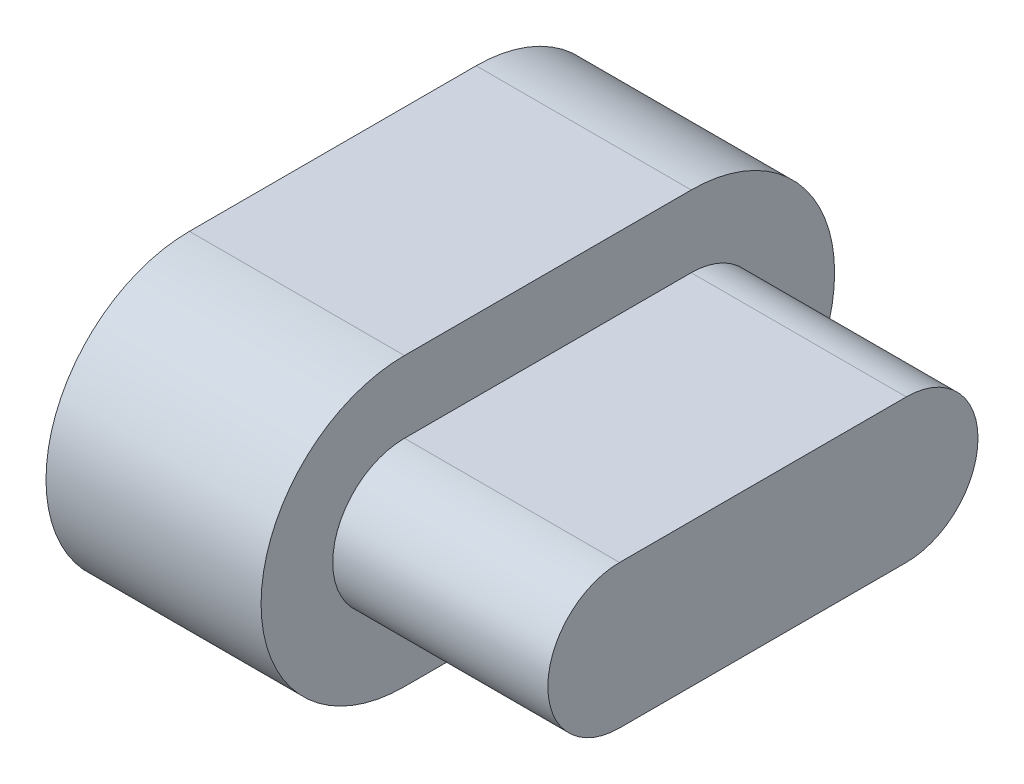
SolidWorks part; units mm, degrees
ref_plane "前视基准面" through (0, 0, 0) normal (0, 0, 1) x (1, 0, 0)
ref_plane "上视基准面" through (0, 0, 0) normal (0, 1, 0) x (1, 0, 0)
ref_plane "右视基准面" through (0, 0, 0) normal (1, 0, 0) x (0, 0, -1)
sketch "草图1" plane through (0, 0, 0) normal (1, 0, 0) x (0, 0, -1)
  line L0 (-2, 0) -> (2, 0) construction
  line L1 (-2, 2) -> (2, 2)
  line L2 (-2, -2) -> (2, -2)
  arc A0 (-2, 2) -> (-2, -2) centre (-2, 0) ccw
  arc A1 (2, -2) -> (2, 2) centre (2, 0) ccw
  point P3 (0, 0)
  dimension "D2" = 2
  dimension "D1" = 4
extrude "凸台-拉伸1" add sketch "草图1" along normal blind 3
sketch "草图2" plane through (3, 0, 0) normal (1, 0, 0) x (0, 0, -1)
  line L4 (-2, -1) -> (2, -1)
  line L5 (2, 1) -> (-2, 1)
  line L6 (-2, -1) -> (2, -1)
  line L7 (2, 1) -> (-2, 1)
  arc A4 (-2, 1) -> (-2, -1) centre (-2, 0) ccw
  arc A5 (2, -1) -> (2, 1) centre (2, 0) ccw
  arc A6 (-2, 1) -> (-2, -1) centre (-2, 0) ccw
  arc A7 (2, -1) -> (2, 1) centre (2, 0) ccw
  dimension "D1" = 1
extrude "凸台-拉伸2" add sketch "草图2" along normal blind 3
